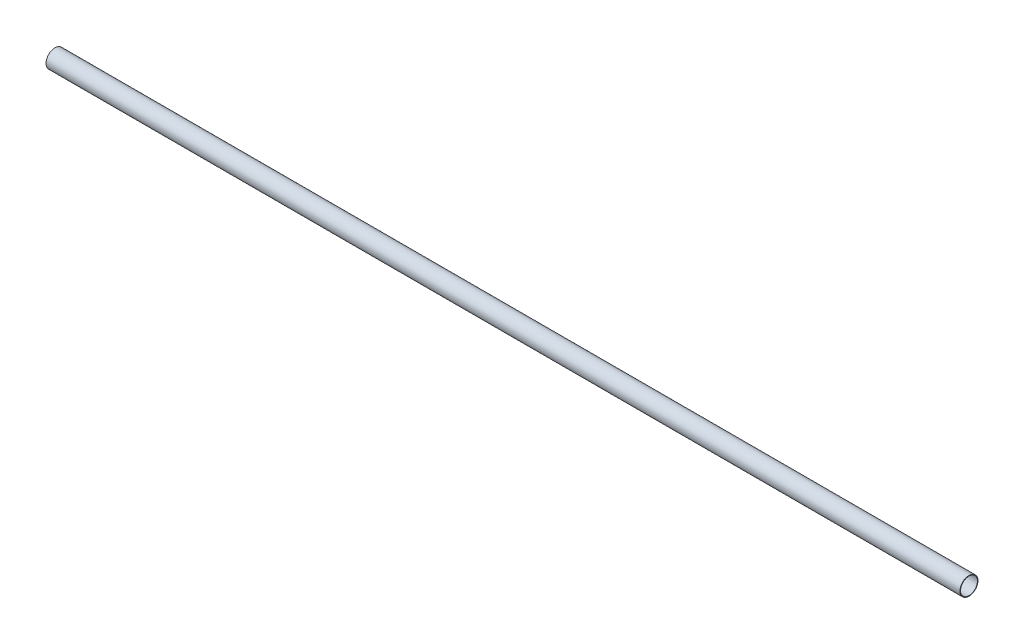
SolidWorks part; units mm, degrees
material "Copper"
ref_plane "Front" through (0, 0, 0) normal (0, 0, 1) x (1, 0, 0)
ref_plane "Top" through (0, 0, 0) normal (0, 1, 0) x (1, 0, 0)
ref_plane "Right" through (0, 0, 0) normal (1, 0, 0) x (0, 0, -1)
sketch "Sketch1" plane through (0, 0, 0) normal (1, 0, 0) x (0, 0, -1)
  circle A0 centre (0, 0) radius 14.2875
  circle A1 centre (0, 0) radius 13.3985
  point P4 (14.2875, 0)
  point P5 (13.3985, 0)
  dimension "OD" = 28.575
  dimension "ID" = 26.797
  dimension "Wall" = 0.889
extrude "Extrude1" add sketch "Sketch1" along normal mid plane 1447.8
sketch "Sketch2" plane through (0, 0, 0) normal (0, 0, 1) x (1, 0, 0)
  line L0 (-723.9, 0) -> (723.9, 0) construction
  line L1 (-723.9, 14.2875) -> (-723.9, -14.2875) construction
